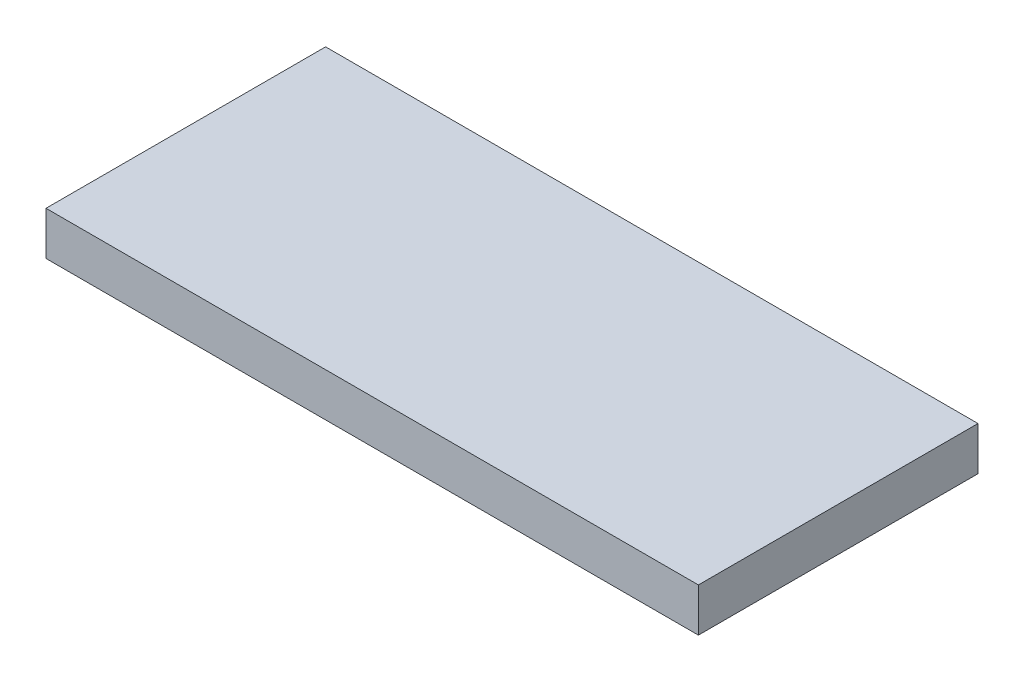
SolidWorks part; units mm, degrees
ref_plane "Plan de face" through (0, 0, 0) normal (0, 0, 1) x (1, 0, 0)
ref_plane "Plan de dessus" through (0, 0, 0) normal (0, 1, 0) x (1, 0, 0)
ref_plane "Plan de droite" through (0, 0, 0) normal (1, 0, 0) x (0, 0, -1)
sketch "Esquisse1" plane through (0, 0, 0) normal (0, 1, 0) x (1, 0, 0)
  line L1 (0, 0) -> (150, 0)
  line L2 (0, 0) -> (0, 64.2857)
  line L3 (0, 64.2857) -> (150, 64.2857)
  line L4 (150, 0) -> (150, 64.2857)
  dimension "D1" = 150
  dimension "D2" = 64.2857
extrude "Boss.-Extru.1" add sketch "Esquisse1" along normal blind 10
